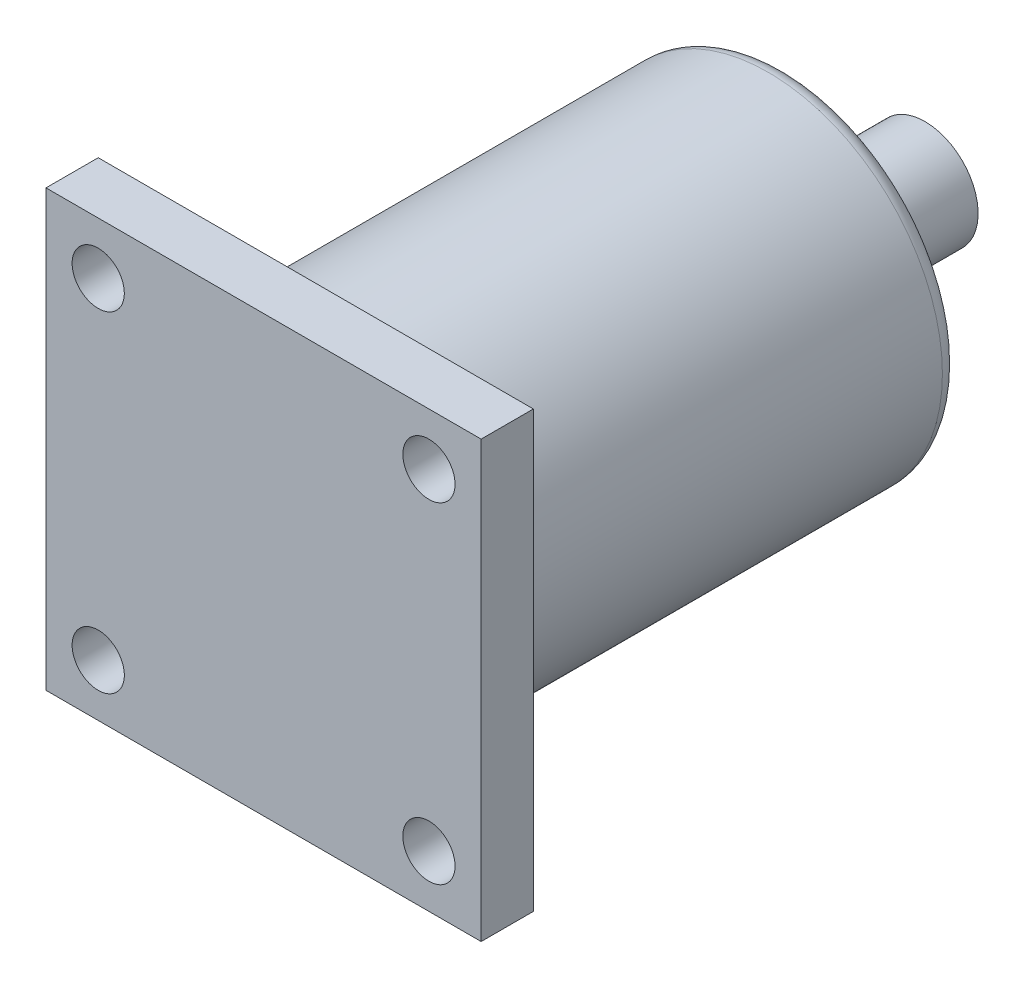
SolidWorks part; units mm, degrees
ref_plane "前视基准面" through (0, 0, 0) normal (0, 0, 1) x (1, 0, 0)
ref_plane "上视基准面" through (0, 0, 0) normal (0, 1, 0) x (1, 0, 0)
ref_plane "右视基准面" through (0, 0, 0) normal (1, 0, 0) x (0, 0, -1)
sketch "草图2" plane through (0, 0, 0) normal (0, 0, 1) x (1, 0, 0)
  line L1 (0, 0) -> (25, 0)
  line L2 (0, 0) -> (0, -25)
  line L3 (0, -25) -> (25, -25)
  line L4 (25, 0) -> (25, -25)
  dimension "D1" = 25
  dimension "D2" = 25
extrude "凸台-拉伸1" add sketch "草图2" along normal blind 3
sketch "草图3" plane through (0, 0, 0) normal (0, 0, -1) x (-1, 0, 0)
  line L0 (-12.5, 0) -> (-12.5, -16.674) construction
  line L1 (-25, 0) -> (0, 0) construction
  line L2 (-25, -12.5) -> (0, -12.5) construction
  line L3 (-25, -25) -> (-25, 0) construction
  line L4 (0, 0) -> (0, -25) construction
  circle A0 centre (-22, -3) radius 1.5
  circle A1 centre (-3, -3) radius 1.5
  circle A2 centre (-3, -22) radius 1.5
  circle A3 centre (-22, -22) radius 1.5
  dimension "D3" = 3
  dimension "D1" = 3
  dimension "D2" = 3
extrude "切除-拉伸2" cut sketch "草图3" against normal through all
sketch "草图4" plane through (0, 0, 3) normal (0, 0, 1) x (1, 0, 0)
  line L0 (0, 0) -> (25, -25) construction
  line L7 (19, -19) -> (6, -6) construction
  circle A0 centre (12.5, -12.5) radius 10
  point P4 (12.5, -12.5)
  dimension "D1" = 20
extrude "凸台-拉伸2" add sketch "草图4" against normal blind 27 from surface at -3 starting at face at (23.5, -22, 0)
sketch "草图5" plane through (0, 0, -27) normal (0, 0, -1) x (-1, 0, 0)
  line L0 (-21.2215, -17.3924) -> (-3.7785, -7.6076) construction
  circle A3 centre (-12.5, -12.5) radius 10 construction
  circle A4 centre (-12.5, -12.5) radius 3.05
  dimension "D1" = 6.1
extrude "凸台-拉伸3" add sketch "草图5" along normal blind 8
fillet "圆角3" radius 1 2 edges at (22.5, -12.5, -27) (22.5, -12.5, 0)
